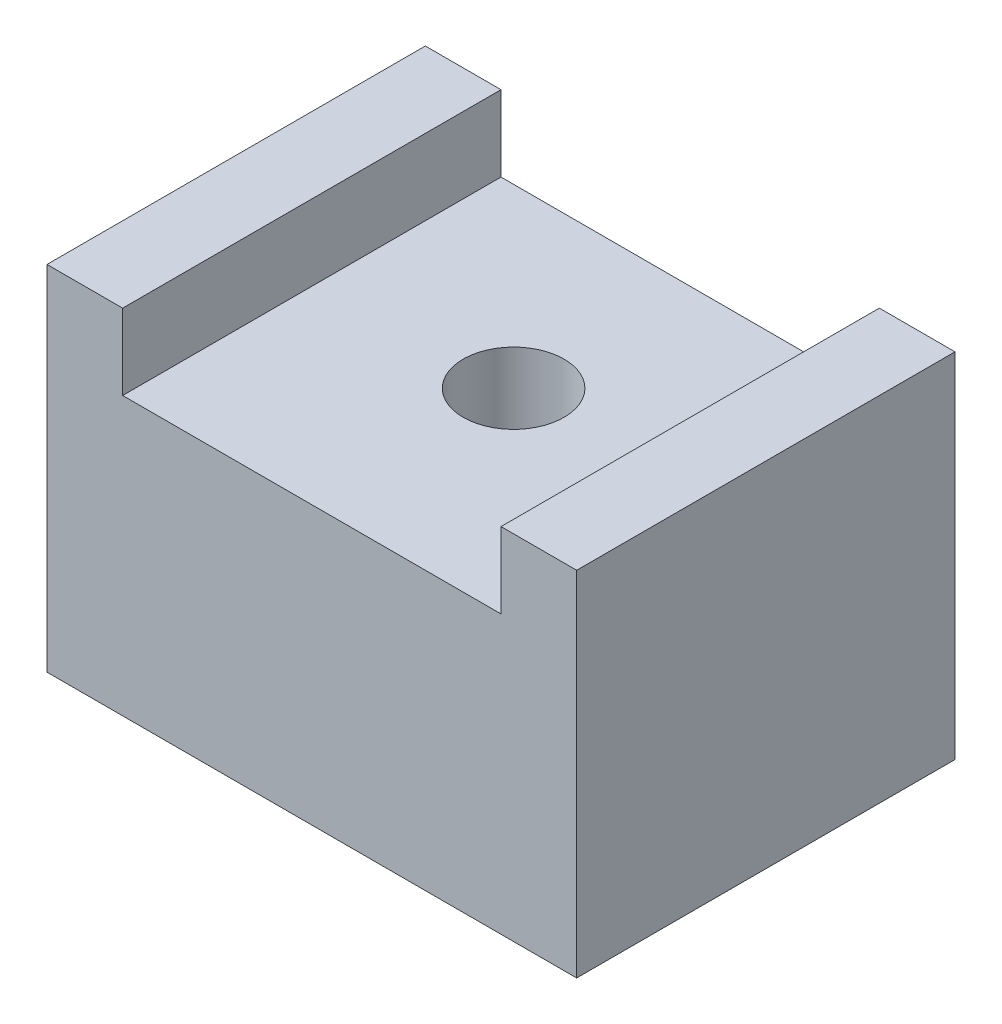
SolidWorks part; units mm, degrees
ref_plane "Front Plane" through (0, 0, 0) normal (0, 0, 1) x (1, 0, 0)
ref_plane "Top Plane" through (0, 0, 0) normal (0, 1, 0) x (1, 0, 0)
ref_plane "Right Plane" through (0, 0, 0) normal (1, 0, 0) x (0, 0, -1)
sketch "Sketch1" plane through (0, 0, 0) normal (0, 0, 1) x (1, 0, 0)
  line L0 (7.5, 0) -> (-7.5, 0)
  line L1 (-7.5, 0) -> (-7.5, 3)
  line L2 (-7.5, 3) -> (-10.5, 3)
  line L3 (-10.5, 3) -> (-10.5, -11)
  line L4 (-10.5, -11) -> (10.5, -11)
  line L5 (10.5, -11) -> (10.5, 3)
  line L6 (10.5, 3) -> (7.5, 3)
  line L7 (7.5, 3) -> (7.5, 0)
  point P4 (0, 0)
  dimension "D1" = 15
  dimension "D2" = 11
  dimension "D3" = 3
  dimension "D4" = 3
extrude "Boss-Extrude1" add sketch "Sketch1" along normal blind 15
sketch "Sketch2" plane through (0, 0, 0) normal (0, 1, 0) x (1, 0, 0)
  line L0 (0, 0) -> (0, -15) construction
  line L1 (7.5, 0) -> (-7.5, 0) construction
  line L2 (7.5, -15) -> (-7.5, -15) construction
  circle A0 centre (0, -7) radius 2
  point P8 (0, -9)
  dimension "D1" = 4
  dimension "D2" = 7
extrude "Cut-Extrude1" cut sketch "Sketch2" against normal up to surface (11 mm away) up to face at (0, -11, 7.5)
